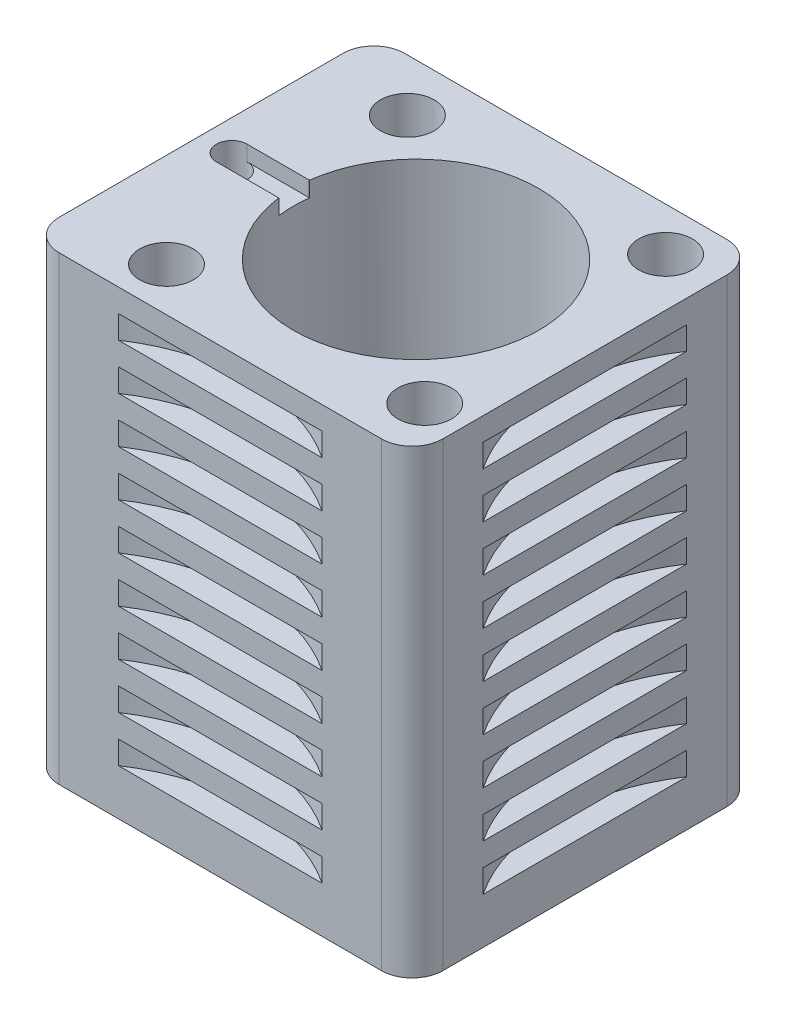
SolidWorks part; units mm, degrees
material "6061 Alloy"
ref_plane "Front Plane" through (0, 0, 0) normal (0, 0, 1) x (1, 0, 0)
ref_plane "Top Plane" through (0, 0, 0) normal (0, 1, 0) x (1, 0, 0)
ref_plane "Right Plane" through (0, 0, 0) normal (1, 0, 0) x (0, 0, -1)
sketch "Sketch1" plane through (0, 0, 0) normal (0, 1, 0) x (1, 0, 0)
  line L0 (-35.5563, 0) -> (37.9648, 0) construction
  line L1 (-21, -22.5) -> (21, -22.5)
  line L2 (-25, -18.5) -> (-25, 18.5)
  line L3 (-21, 22.5) -> (21, 22.5)
  line L4 (25, -18.5) -> (25, 18.5)
  line L5 (-25, -22.5) -> (25, 22.5) construction
  line L6 (-25, 22.5) -> (25, -22.5) construction
  line L7 (3, 25.9542) -> (3, -25.1303) construction
  line L8 (-21, 0) -> (-15.2695, 0) construction
  circle A1 centre (3, 0) radius 23 construction
  arc A2 (21, 22.5) -> (25, 18.5) centre (21, 18.5) cw
  arc A3 (21, -22.5) -> (25, -18.5) centre (21, -18.5) ccw
  arc A4 (-21, -22.5) -> (-25, -18.5) centre (-21, -18.5) cw
  arc A5 (-25, 18.5) -> (-21, 22.5) centre (-21, 18.5) cw
  circle A6 centre (18.688, 16.8192) radius 3.5
  circle A7 centre (19.8192, -15.688) radius 3.5
  circle A8 centre (-12.688, -16.8192) radius 3.5
  circle A9 centre (-13.8192, 15.688) radius 3.5
  circle A14 centre (3, 0) radius 16
  point P0 (0, 0)
  point P35 (3, 0)
  dimension "D3" = 22
  dimension "D4" = 46
  dimension "D5" = 4
  dimension "D6" = 7
  dimension "D11" = 24
  dimension "D10" = 32
  dimension "D1" = 50
  dimension "D2" = 45
  dimension "D8" = 23
  dimension "D9" = 23
  dimension "D17" = 15.2695
  dimension "D7" = 4
extrude "Boss-Extrude2" add sketch "Sketch1" along normal blind 60
sketch "Sketch6" plane through (0, 60, 0) normal (0, 1, 0) x (1, 0, 0)
  line L0 (-21, 0) -> (-13, 0) construction
  line L1 (-21, 2) -> (-13, 2)
  line L2 (-21, -2) -> (-13, -2)
  arc A0 (-21, 2) -> (-21, -2) centre (-21, 0) ccw
  arc A1 (-13, -2) -> (-12.875, -1.9961) centre (-13, 0) ccw
  circle A2 centre (3, 0) radius 16 construction
  circle A3 centre (3, 0) radius 16 construction
  arc A4 (-12.875, 1.9961) -> (-13, 2) centre (-13, 0) ccw
  point P3 (-17, 0)
  circle M19 centre (3, 0) radius 16
  dimension "D2" = 4
  dimension "D7" = 2
  dimension "D1" = 24
  dimension "D3" = 8
  dimension "D4" = 4
  dimension "D5" = 17
  dimension "D6" = 162.508
  dimension "D8" = 8
extrude "Cut-Extrude6" cut sketch "Sketch6" against normal blind 2 and the other way through all contours A4 L1 A0 L2 A1 M19
sketch "Sketch7" plane through (0, 58, 0) normal (0, 1, 0) x (1, 0, 0)
  circle A0 centre (-21, 0) radius 2
extrude "Cut-Extrude7" cut sketch "Sketch7" against normal through all
sketch "Sketch8" plane through (0, 0, 0) normal (0, -1, 0) x (1, 0, 0)
  circle A0 centre (3, 0) radius 16
  circle A1 centre (3, 0) radius 18
  dimension "D1" = 36
  dimension "D2" = 32
extrude "Boss-Extrude3" add sketch "Sketch8" along normal blind 2
sketch "Sketch9" plane through (0, 0, 0) normal (0, 1, 0) x (1, 0, 0)
  line L0 (0, 0) -> (42.9077, 0) construction
  line L1 (25, -18.5) -> (25, 18.5) construction
  line L4 (21, 22.5) -> (-21, 22.5) construction
  circle A0 centre (45, 0) radius 24
  circle A1 centre (0, 42.5) radius 24
  circle A2 centre (0, -42.5) radius 24
  dimension "D1" = 48
  dimension "D4" = 48
  dimension "D2" = 20
  dimension "D3" = 20
extrude "Cut-Extrude8" cut sketch "Sketch9" along normal blind 3 from offset 6
pattern_linear "LPattern1" count 9 spacing 6 along (0, 1, 0) of "Cut-Extrude8"
